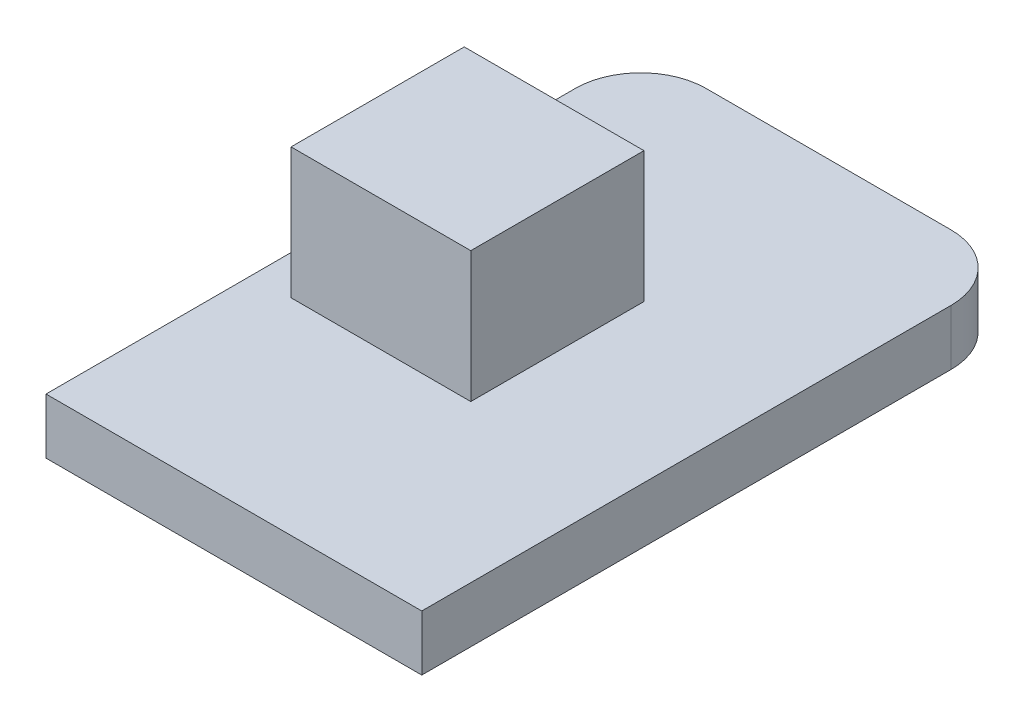
SolidWorks part; units mm, degrees
ref_plane "Front Plane" through (0, 0, 0) normal (0, 0, 1) x (1, 0, 0)
ref_plane "Top Plane" through (0, 0, 0) normal (0, 1, 0) x (1, 0, 0)
ref_plane "Right Plane" through (0, 0, 0) normal (1, 0, 0) x (0, 0, -1)
sketch "Sketch1" plane through (0, 0, 0) normal (0, 1, 0) x (1, 0, 0)
  line L1 (-3.75, 9.1) -> (3.75, 9.1)
  line L2 (-5.75, 7.1) -> (-5.75, -9.1)
  line L3 (-5.75, -9.1) -> (5.75, -9.1)
  line L4 (5.75, 7.1) -> (5.75, -9.1)
  line L5 (-5.75, 9.1) -> (5.75, -9.1) construction
  line L6 (-5.75, -9.1) -> (5.75, 9.1) construction
  arc A0 (3.75, 9.1) -> (5.75, 7.1) centre (3.75, 7.1) cw
  arc A1 (-3.75, 9.1) -> (-5.75, 7.1) centre (-3.75, 7.1) ccw
  point P0 (0, 0)
  dimension "D3" = 2
  dimension "D1" = 18.2
  dimension "D2" = 11.5
extrude "Boss-Extrude1" add sketch "Sketch1" along normal blind 1.7
sketch "Sketch2" plane through (0, 1.7, 0) normal (0, 1, 0) x (1, 0, 0)
  line L0 (3.75, 9.1) -> (-3.75, 9.1) construction
  line L1 (-4.55, 2.5) -> (0.95, 2.5)
  line L2 (-4.55, 2.5) -> (-4.55, -2.8)
  line L3 (-4.55, -2.8) -> (0.95, -2.8)
  line L4 (0.95, 2.5) -> (0.95, -2.8)
  line L5 (5.75, -9.1) -> (5.75, 7.1) construction
  line L6 (-5.75, 7.1) -> (-5.75, -9.1) construction
  line L7 (-5.75, -9.1) -> (5.75, -9.1) construction
  dimension "D1" = 6.6
  dimension "D2" = 4.8
  dimension "D3" = 1.2
  dimension "D4" = 6.3
extrude "Boss-Extrude2" add sketch "Sketch2" along normal blind 4
